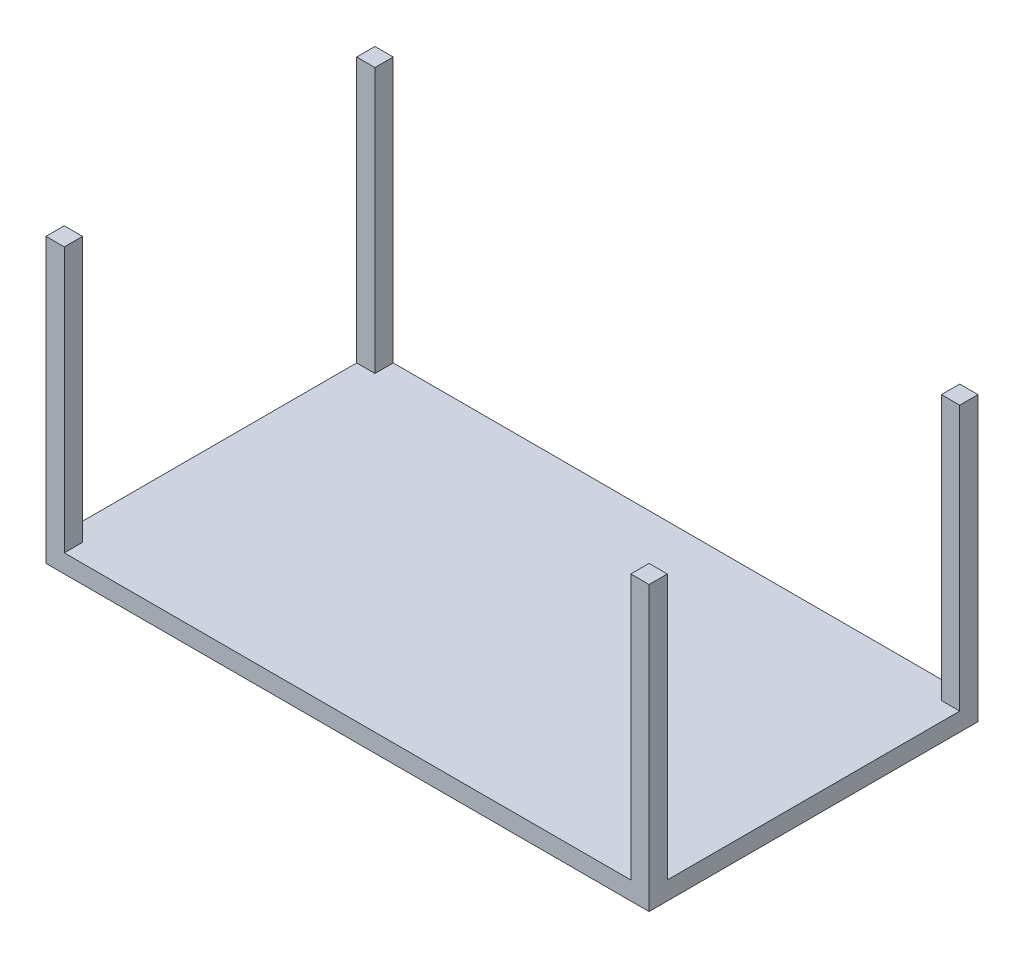
SolidWorks part; units mm, degrees
ref_plane "Front Plane" through (0, 0, 0) normal (0, 0, 1) x (1, 0, 0)
ref_plane "Top Plane" through (0, 0, 0) normal (0, 1, 0) x (1, 0, 0)
ref_plane "Right Plane" through (0, 0, 0) normal (1, 0, 0) x (0, 0, -1)
sketch "Sketch1" plane through (0, 0, 0) normal (0, 1, 0) x (1, 0, 0)
  line L1 (-838.2, -457.2) -> (838.2, -457.2)
  line L2 (-838.2, -457.2) -> (-838.2, 457.2)
  line L3 (-838.2, 457.2) -> (838.2, 457.2)
  line L4 (838.2, -457.2) -> (838.2, 457.2)
  line L5 (-838.2, -457.2) -> (838.2, 457.2) construction
  line L6 (-838.2, 457.2) -> (838.2, -457.2) construction
  point P0 (0, 0)
  dimension "D1" = 914.4
  dimension "D2" = 1676.4
extrude "Boss-Extrude1" add sketch "Sketch1" along normal blind 50.8
sketch "Sketch2" plane through (0, 50.8, 0) normal (0, 1, 0) x (1, 0, 0)
  line L1 (-838.2, 457.2) -> (-787.4, 457.2)
  line L2 (-838.2, 457.2) -> (-838.2, 406.4)
  line L3 (-838.2, 406.4) -> (-787.4, 406.4)
  line L4 (-787.4, 457.2) -> (-787.4, 406.4)
  line L5 (838.2, 457.2) -> (787.4, 457.2)
  line L6 (838.2, 457.2) -> (838.2, 406.4)
  line L7 (838.2, 406.4) -> (787.4, 406.4)
  line L8 (787.4, 457.2) -> (787.4, 406.4)
  line L9 (838.2, -457.2) -> (787.4, -457.2)
  line L10 (838.2, -457.2) -> (838.2, -406.4)
  line L11 (838.2, -406.4) -> (787.4, -406.4)
  line L12 (787.4, -457.2) -> (787.4, -406.4)
  line L13 (-838.2, -457.2) -> (-787.4, -457.2)
  line L14 (-838.2, -457.2) -> (-838.2, -406.4)
  line L15 (-838.2, -406.4) -> (-787.4, -406.4)
  line L16 (-787.4, -457.2) -> (-787.4, -406.4)
  dimension "D1" = 50.8
extrude "Boss-Extrude2" add sketch "Sketch2" along normal blind 736.6
